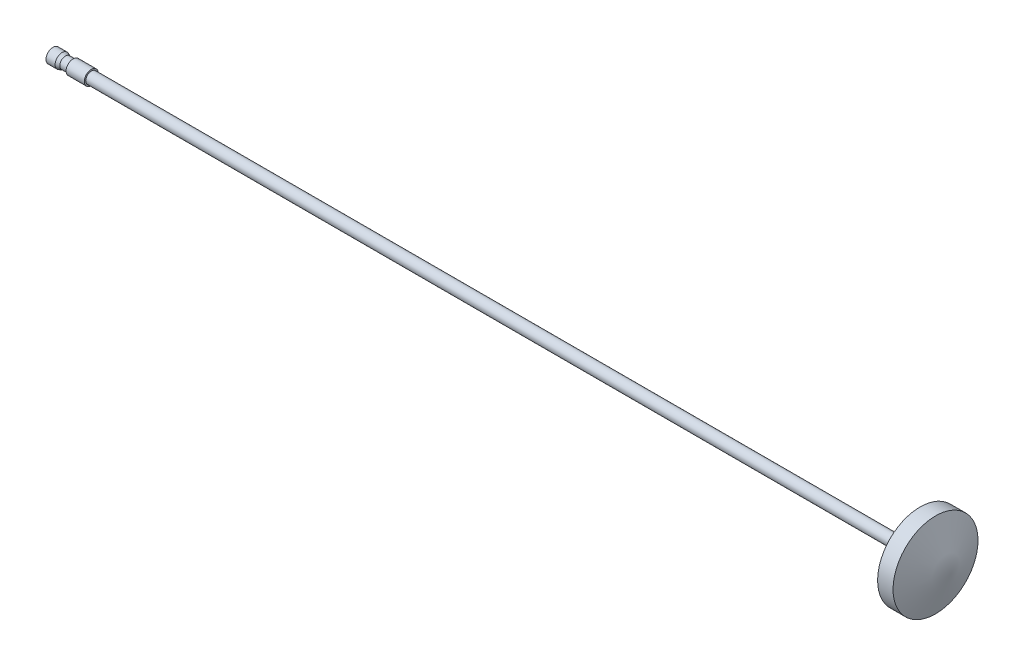
SolidWorks part; units mm, degrees
ref_plane "Front Plane" through (0, 0, 0) normal (0, 0, 1) x (1, 0, 0)
ref_plane "Top Plane" through (0, 0, 0) normal (0, 1, 0) x (1, 0, 0)
ref_plane "Right Plane" through (0, 0, 0) normal (1, 0, 0) x (0, 0, -1)
sketch "Sketch1" plane through (0, 0, 0) normal (0, 0, 1) x (1, 0, 0)
  line L0 (-49.42, 0) -> (49.42, 0) construction
  line L1 (-49.42, 0.625) -> (49.42, 0.625) construction
  line L2 (-49.42, 0.625) -> (-49.42, -0.625) construction
  line L3 (-49.42, -0.625) -> (49.42, -0.625) construction
  line L4 (49.42, 0.625) -> (49.42, -0.625) construction
  line L5 (-49.42, 0.625) -> (49.42, -0.625) construction
  line L6 (-49.42, -0.625) -> (49.42, 0.625) construction
  line L7 (-49.42, 0.625) -> (-49.4069, 0.775) construction
  line L8 (-49.4069, 0.775) -> (-48.4069, 0.775) construction
  line L9 (-48.4069, 0.775) -> (-48.04, 0.625) construction
  line L10 (-47.21, 0.625) -> (-47.1969, 0.775) construction
  line L11 (-47.1969, 0.775) -> (-45.1969, 0.775) construction
  line L12 (-45.1969, 0.775) -> (-45.1838, 0.625) construction
  line L13 (-48.04, 0.625) -> (-47.21, 0.625)
  line L14 (49.42, 0) -> (46.02, 0) construction
  line L15 (46.02, 4.675) -> (49.42, 4.675) construction
  line L16 (46.02, 4.675) -> (46.02, -4.675) construction
  line L17 (46.02, -4.675) -> (49.42, -4.675) construction
  line L18 (49.42, 4.675) -> (49.42, -4.675) construction
  line L19 (-49.42, 0.625) -> (-49.4069, 0.775)
  line L20 (-49.4069, 0.775) -> (-48.4069, 0.775)
  line L21 (-48.4069, 0.775) -> (-48.04, 0.625)
  line L22 (-45.1838, 0.625) -> (-45.1969, 0.775)
  line L23 (-47.21, 0.625) -> (-47.1969, 0.775)
  line L24 (-47.1969, 0.775) -> (-45.1969, 0.775)
  line L25 (46.02, 0.625) -> (-45.1838, 0.625)
  line L26 (46.02, 0.625) -> (46.02, 4.675)
  line L27 (49.42, 0) -> (47.72, 4.675) construction
  line L28 (-49.42, 0.625) -> (-49.42, 0)
  line L29 (-49.42, 0) -> (49.42, 0)
  line L30 (49.42, 0) -> (47.72, 4.675)
  line L31 (47.72, 4.675) -> (46.02, 4.675)
  point P0 (0, 0)
  point P13 (-48.9069, 0.775)
  dimension "D1" = 98.84
  dimension "D2" = 1.25
  dimension "D3" = 0.15
  dimension "D4" = 1.38
  dimension "D5" = 1
  dimension "D6" = 85
  dimension "D7" = 0.83
  dimension "D8" = 2
  dimension "D9" = 85
  dimension "D10" = 85
  dimension "D11" = 9.35
  dimension "D12" = 3.4
revolve "Revolve1" add sketch "Sketch1" angle 360 about L29
